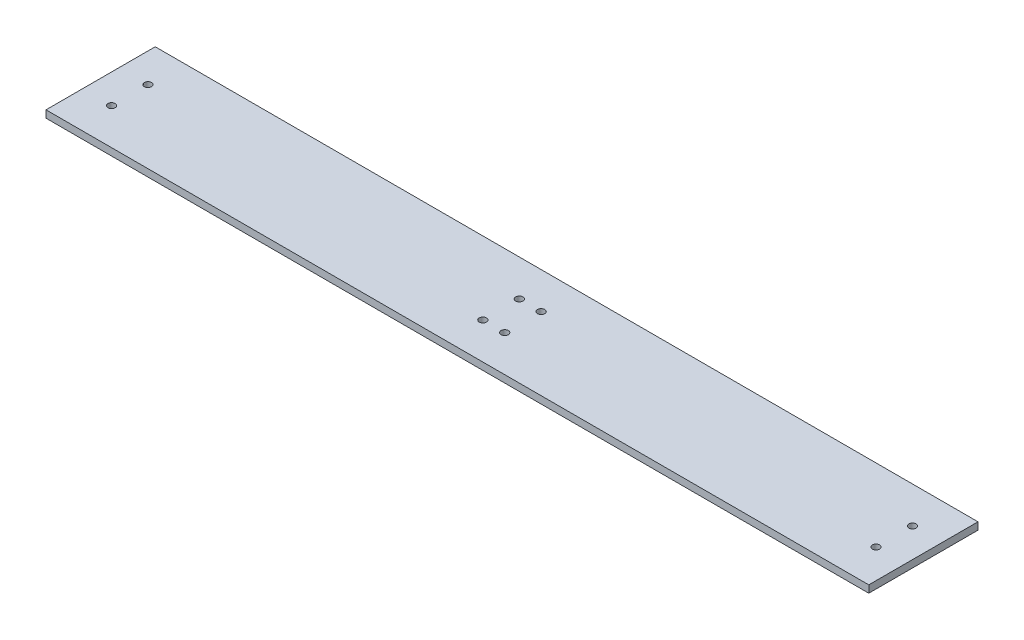
SolidWorks part; units mm, degrees
ref_plane "Спереди" through (0, 0, 0) normal (0, 0, 1) x (1, 0, 0)
ref_plane "Сверху" through (0, 0, 0) normal (0, 1, 0) x (1, 0, 0)
ref_plane "Справа" through (0, 0, 0) normal (1, 0, 0) x (0, 0, -1)
sketch "Эскиз1" plane through (0, 0, 0) normal (1, 0, 0) x (0, 0, -1)
  line L1 (0, 0) -> (150, 0)
  line L2 (0, 0) -> (0, 10)
  line L3 (0, 10) -> (150, 10)
  line L4 (150, 0) -> (150, 10)
extrude "Бобышка-Вытянуть1" add sketch "Эскиз1" along normal blind 1130
sketch "Эскиз2" plane through (0, 10, 0) normal (0, 1, 0) x (1, 0, 0)
  line L0 (565, 150) -> (565, 0) construction
  line L1 (1130, 150) -> (0, 150) construction
  line L2 (1130, 0) -> (0, 0) construction
  circle A0 centre (40, 50) radius 5
  circle A1 centre (550, 50) radius 5
  circle A2 centre (550, 100) radius 5
  circle A3 centre (40, 100) radius 5
  circle A4 centre (1090, 100) radius 5
  circle A5 centre (580, 100) radius 5
  circle A6 centre (580, 50) radius 5
  circle A7 centre (1090, 50) radius 5
  dimension "D1" = 2
  dimension "D2" = 2
extrude "Вырез-Вытянуть1" cut sketch "Эскиз2" against normal through all
